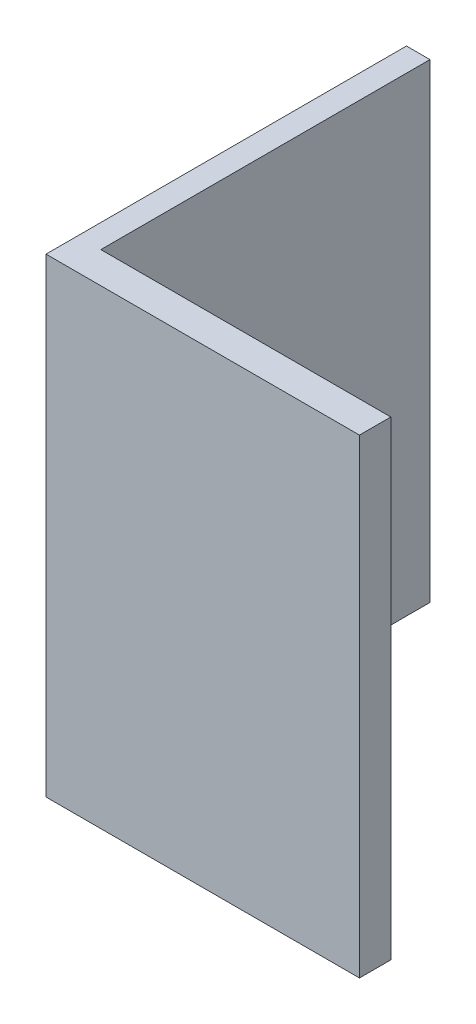
SolidWorks part; units mm, degrees
ref_plane "前视基准面" through (0, 0, 0) normal (0, 0, 1) x (1, 0, 0)
ref_plane "上视基准面" through (0, 0, 0) normal (0, 1, 0) x (1, 0, 0)
ref_plane "右视基准面" through (0, 0, 0) normal (1, 0, 0) x (0, 0, -1)
sketch "草图1" plane through (0, 0, 0) normal (0, 1, 0) x (1, 0, 0)
  line L0 (-16.6056, 20.9432) -> (-16.6056, -2.0568)
  line L1 (-16.6056, -2.0568) -> (3.3944, -2.0568)
  line L2 (3.3944, -2.0568) -> (3.3944, -0.0568)
  line L3 (3.3944, -0.0568) -> (-15.1056, -0.0568)
  line L4 (-15.1056, -0.0568) -> (-15.1056, 20.9432)
  line L5 (-15.1056, 20.9432) -> (-16.6056, 20.9432)
extrude "凸台-拉伸1" add sketch "草图1" along normal blind 30
